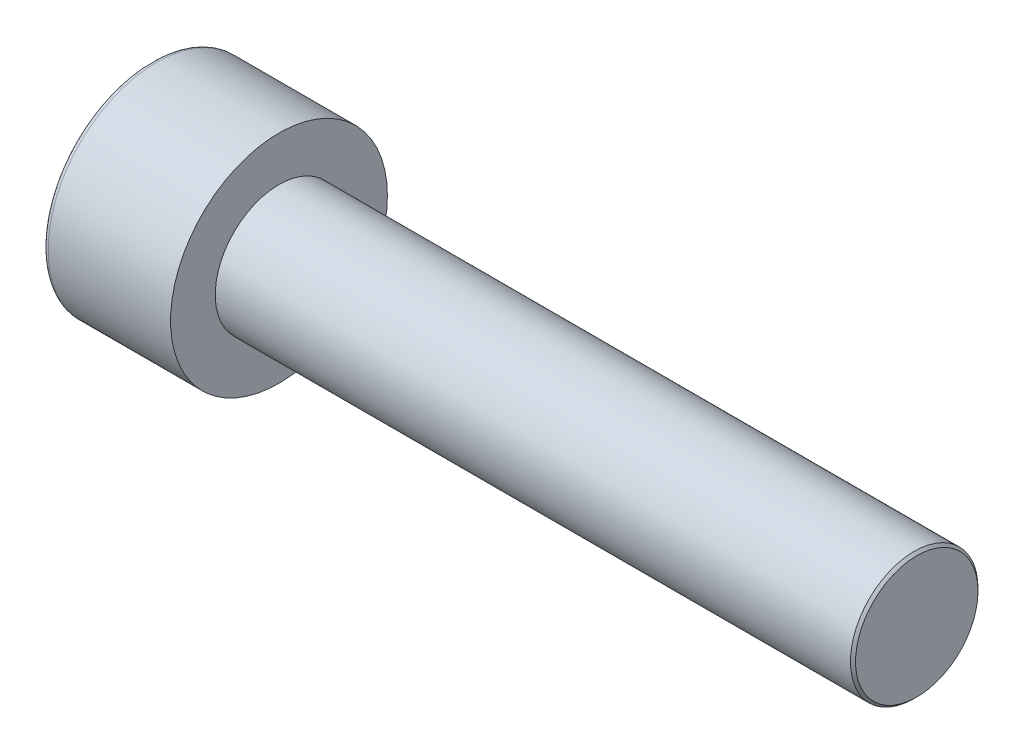
SolidWorks part; units mm, degrees
ref_plane "Front" through (0, 0, 0) normal (0, 0, 1) x (1, 0, 0)
ref_plane "Top" through (0, 0, 0) normal (0, 1, 0) x (1, 0, 0)
ref_plane "Right" through (0, 0, 0) normal (1, 0, 0) x (0, 0, -1)
sketch "Sketch1" plane through (0, 0, 0) normal (1, 0, 0) x (0, 0, -1)
  circle A0 centre (0, 0) radius 4.25
  dimension "dk" = 8.5
extrude "BaseHead" add sketch "Sketch1" along normal blind 5
sketch "Sketch2" plane through (5, 0, 0) normal (1, 0, 0) x (0, 0, -1)
  circle A0 centre (0, 0) radius 2.5
  dimension "d" = 5
extrude "BaseBody" add sketch "Sketch2" along normal blind 25
cosmetic thread "ThreadCosmetic1" [suppressed] parameters "b"=25, "D2"=4.134
sketch "Sketch3" plane through (0, 0, 0) normal (1, 0, 0) x (0, 0, -1)
  line L1 (2.3094, 0) -> (1.1547, 2)
  line L2 (1.1547, 2) -> (-1.1547, 2)
  line L3 (-1.1547, 2) -> (-2.3094, 0)
  line L4 (-2.3094, 0) -> (-1.1547, -2)
  line L5 (-1.1547, -2) -> (1.1547, -2)
  line L6 (1.1547, -2) -> (2.3094, 0)
  circle A0 centre (0, 0) radius 2 construction
  dimension "s" = 4
  dimension "e" = 4.6188
extrude "HexagonSocket" cut sketch "Sketch3" along normal blind 2.5
sketch "Sketch4" plane through (-4.1961, 0.75, 0) normal (0, 0, 1) x (-1, 0, 0)
  line L0 (-6.6961, 2.75) -> (-7.8508, 0.75)
  line L2 (-7.8508, 0.75) -> (-6.6961, 0.75)
  line L3 (-6.6961, 0.75) -> (-6.6961, 2.75)
  line L4 (-5.0351, 0.75) -> (0.839, 0.75) construction
  line L5 (-34.1961, 0.75) -> (-9.1961, 0.75) construction
  line L6 (-9.1961, 0.75) -> (-4.1961, 0.75) construction
  dimension "m" = 60
revolve "Cut-Revolve1" cut sketch "Sketch4" angle 360 about L4
fillet "HeadFillet" [suppressed] radius 0.2
fillet "TopFillet" radius 0.2 1 edges at (0, 0, -4.25)
chamfer "Chamfer1" distance 0.1 angle 45 1 edges at (30, 0, -2.5)
sketch "Sketch5" plane through (0, 0, 0) normal (0, 0, 1) x (1, 0, 0)
  line L0 (29.9, 0.6268) -> (30, 0.8)
  line L1 (30, 0.8) -> (30, 1)
  line L2 (30, 1) -> (29.8, 1)
  line L3 (29.8, 1) -> (29.8, 0.8)
  line L4 (29.8, 0.8) -> (29.9, 0.6268)
  line L5 (0, 0) -> (7.8886, 0) construction
  line L6 (29.9, -2.5) -> (29.9, 2.5) construction
  dimension "D1" = 1.6
  dimension "D2" = 0.2
revolve "Cut-Revolve10" [suppressed] cut sketch "Sketch5" angle 360 about L5
pattern_linear "LPattern10" [suppressed] count 12 spacing 0.24 along (1, 0, 0)
equation "\"r1@TopFillet\" = \"d@Sketch2\" / 8"
equation "\"D1@Chamfer1\" = \"r@HeadFillet\""
equation "\"D1@Sketch5\" = \"d@Sketch2\""
equation "\"D2@Sketch5\" =  ( \"d@Sketch2\" - \"D2@ThreadCosmetic1\" )  / 2"
equation "\"D3@LPattern10\" = \"D2@Sketch5\" * 1.2"
equation "\"D1@LPattern10\" = \"b@ThreadCosmetic1\" / \"D3@LPattern10\""
